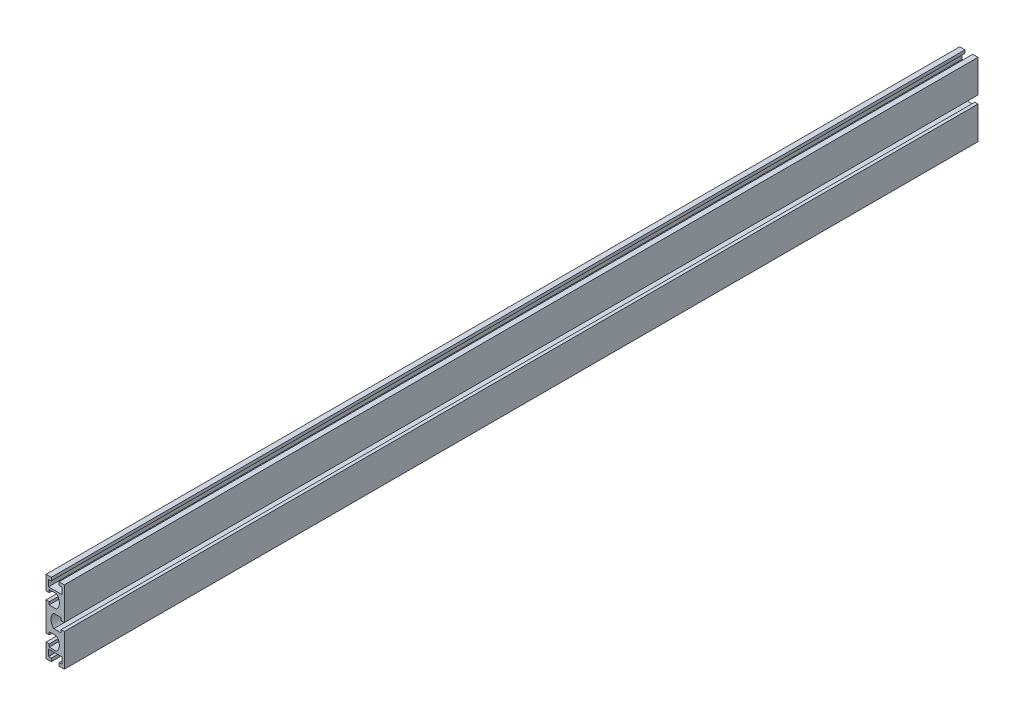
SolidWorks part; units mm, degrees
material "6063 T5"
ref_plane "Спереди" through (0, 0, 0) normal (0, 0, 1) x (1, 0, 0)
ref_plane "Сверху" through (0, 0, 0) normal (0, 1, 0) x (1, 0, 0)
ref_plane "Справа" through (0, 0, 0) normal (1, 0, 0) x (0, 0, -1)
sketch "Эскиз1" plane through (0, 0, 0) normal (0, 0, 1) x (1, 0, 0)
  line L0 (0, 40) -> (0, -40) construction
  line L1 (-10, 0) -> (10, 0) construction
  line L2 (38.6426, 40.7814) -> (38.6426, -39.2186) construction
  line L3 (-10, 27.25) -> (-10, 40)
  line L4 (-10, 40) -> (-4.25, 40)
  line L5 (-4.25, 40) -> (-4.25, 36.6)
  line L6 (-4.25, 36.6) -> (-7.25, 36.6)
  line L7 (-7.25, 36.6) -> (-7.25, 29.5)
  line L8 (-7.25, 29.5) -> (7.25, 29.5)
  line L9 (4.25, 36.6) -> (7.25, 36.6)
  line L10 (7.25, 36.6) -> (7.25, 29.5)
  line L11 (4.25, 40) -> (4.25, 36.6)
  line L12 (4.25, 40) -> (10, 40)
  line L13 (10, 40) -> (10, 7.25)
  line L14 (10, -40) -> (10, -7.25)
  line L15 (4.25, -40) -> (10, -40)
  line L16 (4.25, -40) -> (4.25, -36.6)
  line L17 (4.25, -36.6) -> (7.25, -36.6)
  line L18 (7.25, -36.6) -> (7.25, -29.5)
  line L19 (-7.25, -29.5) -> (7.25, -29.5)
  line L20 (-7.25, -36.6) -> (-7.25, -29.5)
  line L21 (-4.25, -36.6) -> (-7.25, -36.6)
  line L22 (-4.25, -40) -> (-4.25, -36.6)
  line L23 (-10, -40) -> (-4.25, -40)
  line L24 (-10, -27.25) -> (-10, -40)
  line L25 (-10, 12.75) -> (-10, -12.75)
  point P8 (-10, 22.3071)
  point P14 (10, 0)
  point P15 (0, -29.5)
  point P21 (0, 29.5)
  point P37 (-10, 20)
  line B0 (-10, 27.25) -> (-10, 24.25)
  line B1 (-10, 24.25) -> (-6.5, 24.25)
  line B2 (-6.5, 24.25) -> (-6.5, 27.25)
  line B3 (-6.5, 27.25) -> (1.5, 27.25)
  line B4 (1.5, 12.75) -> (-6.5, 12.75)
  line B5 (-6.5, 12.75) -> (-6.5, 15.75)
  line B6 (-6.5, 15.75) -> (-10, 15.75)
  line B7 (-10, 15.75) -> (-10, 12.75)
  line B8 (-10, 27.25) -> (-10, 12.75) construction
  arc B9 (1.5, 27.25) -> (1.5, 12.75) centre (-5.3875, 20) cw
  line B10 (10, -7.25) -> (10, -4.25)
  line B11 (10, -4.25) -> (6.5, -4.25)
  line B12 (6.5, -4.25) -> (6.5, -7.25)
  line B13 (6.5, -7.25) -> (-1.5, -7.25)
  line B14 (-1.5, 7.25) -> (6.5, 7.25)
  line B15 (6.5, 7.25) -> (6.5, 4.25)
  line B16 (6.5, 4.25) -> (10, 4.25)
  line B17 (10, 4.25) -> (10, 7.25)
  line B18 (10, -7.25) -> (10, 7.25) construction
  arc B19 (-1.5, -7.25) -> (-1.5, 7.25) centre (5.3875, 0) cw
  line B20 (-10, -27.25) -> (-10, -24.25)
  line B21 (-10, -24.25) -> (-6.5, -24.25)
  line B22 (-6.5, -24.25) -> (-6.5, -27.25)
  line B23 (-6.5, -27.25) -> (1.5, -27.25)
  line B24 (1.5, -12.75) -> (-6.5, -12.75)
  line B25 (-6.5, -12.75) -> (-6.5, -15.75)
  line B26 (-6.5, -15.75) -> (-10, -15.75)
  line B27 (-10, -15.75) -> (-10, -12.75)
  line B28 (-10, -27.25) -> (-10, -12.75) construction
  arc B29 (1.5, -27.25) -> (1.5, -12.75) centre (-5.3875, -20) ccw
  dimension "D1" = 80
  dimension "D2" = 20
  dimension "D3" = 80
  dimension "D4" = 20
  dimension "D5" = 8.5
  dimension "D6" = 14.5
  dimension "D7" = 3.4
  dimension "D8" = 10.5
sketch_block_instance "6G(10,4С)-1"
sketch_block "6G(10,4С)" parameters "D4"=6.5, "D1"=14.5, "D2"=8.5, "D3"=2.2, "D5"=6
sketch_block_instance "6G(10,4С)-3"
sketch_block_instance "6G(10,4С)-5"
extrude "Бобышка-Вытянуть1" add sketch "Эскиз1" along normal blind 1000
